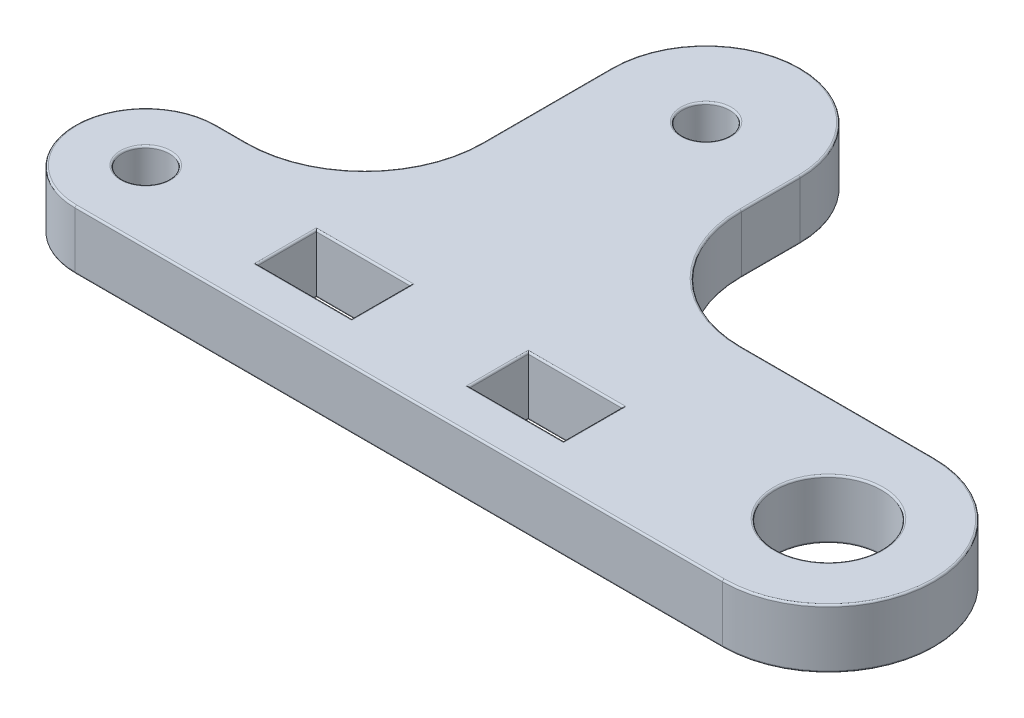
SolidWorks part; units mm, degrees
ref_plane "Ön Düzlem" through (0, 0, 0) normal (0, 0, 1) x (1, 0, 0)
ref_plane "Üst Düzlem" through (0, 0, 0) normal (0, 1, 0) x (1, 0, 0)
ref_plane "Sağ Düzlem" through (0, 0, 0) normal (1, 0, 0) x (0, 0, -1)
sketch "Sketch2" plane through (0, 0, 0) normal (0, 1, 0) x (1, 0, 0)
  line L0 (-27.5, 0) -> (27.5, 0)
  line L1 (-27.5, 12) -> (-24.9, 12)
  line L2 (-14.9, 22) -> (-14.9, 33)
  line L3 (1.1, 33) -> (1.1, 28)
  line L4 (11.1, 18) -> (27.5, 18)
  line L5 (-27.5, 6) -> (-15.5, 6) construction
  line L7 (-15.5, 8.5) -> (-7.5, 8.5)
  line L8 (-15.5, 8.5) -> (-15.5, 3.5)
  line L9 (-15.5, 3.5) -> (-7.5, 3.5)
  line L10 (-7.5, 8.5) -> (-7.5, 3.5)
  line L11 (2.5, 8.5) -> (10.5, 8.5)
  line L12 (2.5, 8.5) -> (2.5, 3.5)
  line L13 (2.5, 3.5) -> (10.5, 3.5)
  line L14 (10.5, 8.5) -> (10.5, 3.5)
  arc A0 (27.5, 0) -> (27.5, 18) centre (27.5, 9) ccw
  arc A1 (-27.5, 0) -> (-27.5, 12) centre (-27.5, 6) cw
  circle A2 centre (-27.5, 6) radius 2
  circle A3 centre (27.5, 9) radius 4.5
  circle A4 centre (-6.9, 33) radius 2
  circle A5 centre (-6.9, 33) radius 8 construction
  arc A6 (-14.9, 33) -> (1.1, 33) centre (-6.9, 33) cw
  arc A7 (1.1, 28) -> (11.1, 18) centre (11.1, 28) ccw
  arc A8 (-24.9, 12) -> (-14.9, 22) centre (-24.9, 22) ccw
  dimension "D2" = 9
  dimension "D3" = 6
  dimension "D4" = 4
  dimension "D5" = 9
  dimension "D6" = 4
  dimension "D9" = 16
  dimension "D10" = 10
  dimension "D1" = 55
  dimension "D7" = 33
  dimension "D8" = 6.9
  dimension "D11" = 12
  dimension "D12" = 8
  dimension "D13" = 5
  dimension "D14" = 10
extrude "Boss-Extrude1" add sketch "Sketch2" along normal mid plane 5
fillet "Fillet1" radius 0.15 42 edges at (10.5, -2.5, -6) (6.5, -2.5, -3.5) (2.5, -2.5, -6) (6.5, -2.5, -8.5) (-7.5, -2.5, -6) (-11.5, -2.5, -3.5) (-15.5, -2.5, -6) (-11.5, -2.5, -8.5) (-6.9, -2.5, -31) (-27.5, -2.5, -4) (0, -2.5, 0) (36.5, -2.5, -9) (19.3, -2.5, -18) (4.0289, -2.5, -20.9289) (1.1, -2.5, -30.5) (-6.9, -2.5, -41) (-14.9, -2.5, -27.5) (-17.8289, -2.5, -14.9289) (-26.2, -2.5, -12) (-33.5, -2.5, -6) (27.5, -2.5, -4.5) (6.5, 2.5, -3.5) (10.5, 2.5, -6) (6.5, 2.5, -8.5) (2.5, 2.5, -6) (-6.9, 2.5, -31) (27.5, 2.5, -4.5) (-27.5, 2.5, -4) (-26.2, 2.5, -12) (-17.8289, 2.5, -14.9289) (-14.9, 2.5, -27.5) (-6.9, 2.5, -41) (1.1, 2.5, -30.5) (4.0289, 2.5, -20.9289) (19.3, 2.5, -18) (36.5, 2.5, -9) (0, 2.5, 0) (-33.5, 2.5, -6) (-11.5, 2.5, -3.5) (-7.5, 2.5, -6) (-11.5, 2.5, -8.5) (-15.5, 2.5, -6)
